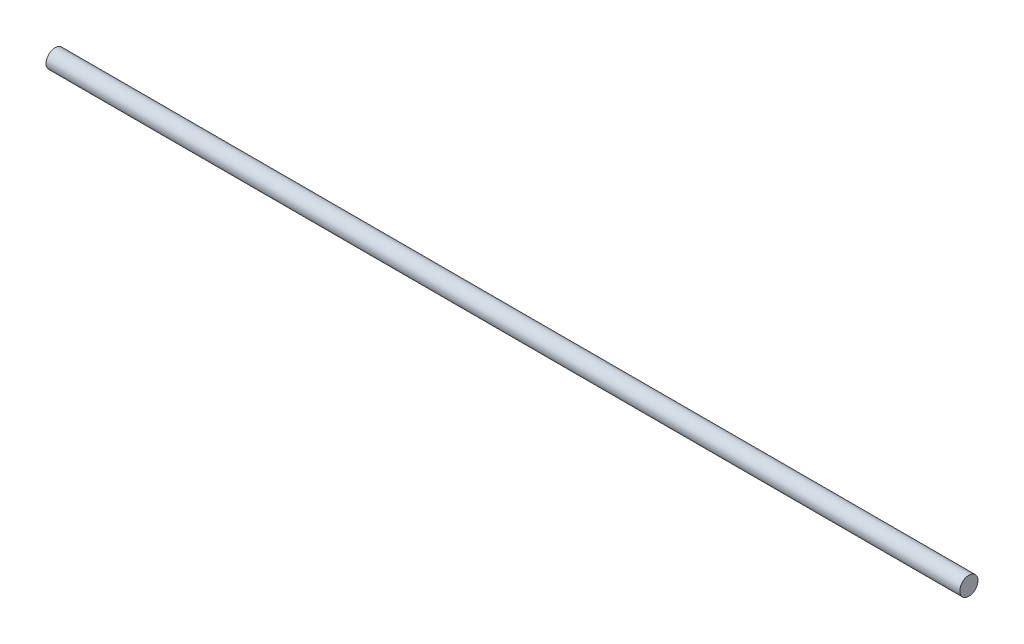
SolidWorks part; units mm, degrees
ref_plane "前视基准面" through (0, 0, 0) normal (0, 0, 1) x (1, 0, 0)
ref_plane "上视基准面" through (0, 0, 0) normal (0, 1, 0) x (1, 0, 0)
ref_plane "右视基准面" through (0, 0, 0) normal (1, 0, 0) x (0, 0, -1)
sketch "草图1" plane through (0, 0, 0) normal (0, 0, 1) x (1, 0, 0)
  line L1 (-25.7312, -4.7866) -> (124.2688, -4.7866)
  line L2 (-25.7312, -4.7866) -> (-25.7312, -6.2866)
  line L3 (-25.7312, -6.2866) -> (124.2688, -6.2866)
  line L4 (124.2688, -4.7866) -> (124.2688, -6.2866)
  dimension "D1" = 150
  dimension "D2" = 1.5
revolve "旋转1" add sketch "草图1" angle 360 about L1
